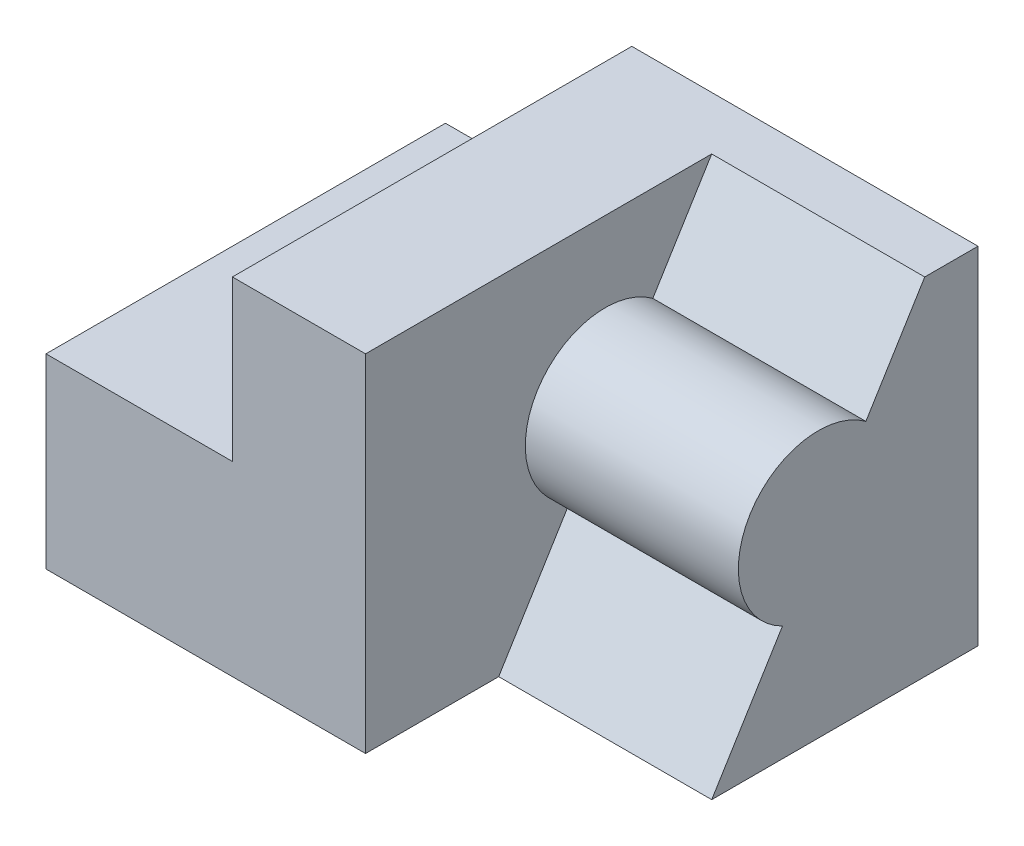
SolidWorks part; units mm, degrees
ref_plane "Front Plane" through (0, 0, 0) normal (0, 0, 1) x (1, 0, 0)
ref_plane "Top Plane" through (0, 0, 0) normal (0, 1, 0) x (1, 0, 0)
ref_plane "Right Plane" through (0, 0, 0) normal (1, 0, 0) x (0, 0, -1)
sketch "Sketch1" plane through (0, 0, 0) normal (0, 1, 0) x (1, 0, 0)
  line L1 (0, 0) -> (100, 0)
  line L2 (0, 0) -> (0, 75)
  line L3 (0, 75) -> (100, 75)
  line L4 (100, 0) -> (100, 75)
  dimension "D1" = 75
  dimension "D2" = 100
extrude "Boss-Extrude1" add sketch "Sketch1" along normal blind 65
sketch "Sketch2" plane through (0, 65, 0) normal (0, 1, 0) x (1, 0, 0)
  line L0 (100, 75) -> (0, 75) construction
  line L1 (0, 0) -> (35, 0)
  line L2 (0, 0) -> (0, 75)
  line L3 (0, 75) -> (35, 75)
  line L4 (35, 0) -> (35, 75)
  dimension "D1" = 35
extrude "Cut-Extrude1" cut sketch "Sketch2" against normal blind 30
sketch "Sketch3" plane through (100, 0, 0) normal (1, 0, 0) x (0, 0, -1)
  line L0 (25, 0) -> (38.2845, 21.5873)
  line L1 (0, 0) -> (75, 0) construction
  line L2 (0, 65) -> (75, 65) construction
  line L3 (53.9473, 47.0394) -> (65, 65)
  line L4 (65, 65) -> (0, 65)
  line L5 (0, 65) -> (0, 0)
  line L6 (0, 0) -> (25, 0)
  arc A0 (53.9473, 47.0394) -> (38.2845, 21.5873) centre (45, 35) ccw
  dimension "D5" = 30
  dimension "D1" = 25
  dimension "D2" = 10
  dimension "D3" = 45
  dimension "D4" = 30
extrude "Cut-Extrude2" cut sketch "Sketch3" against normal blind 40
